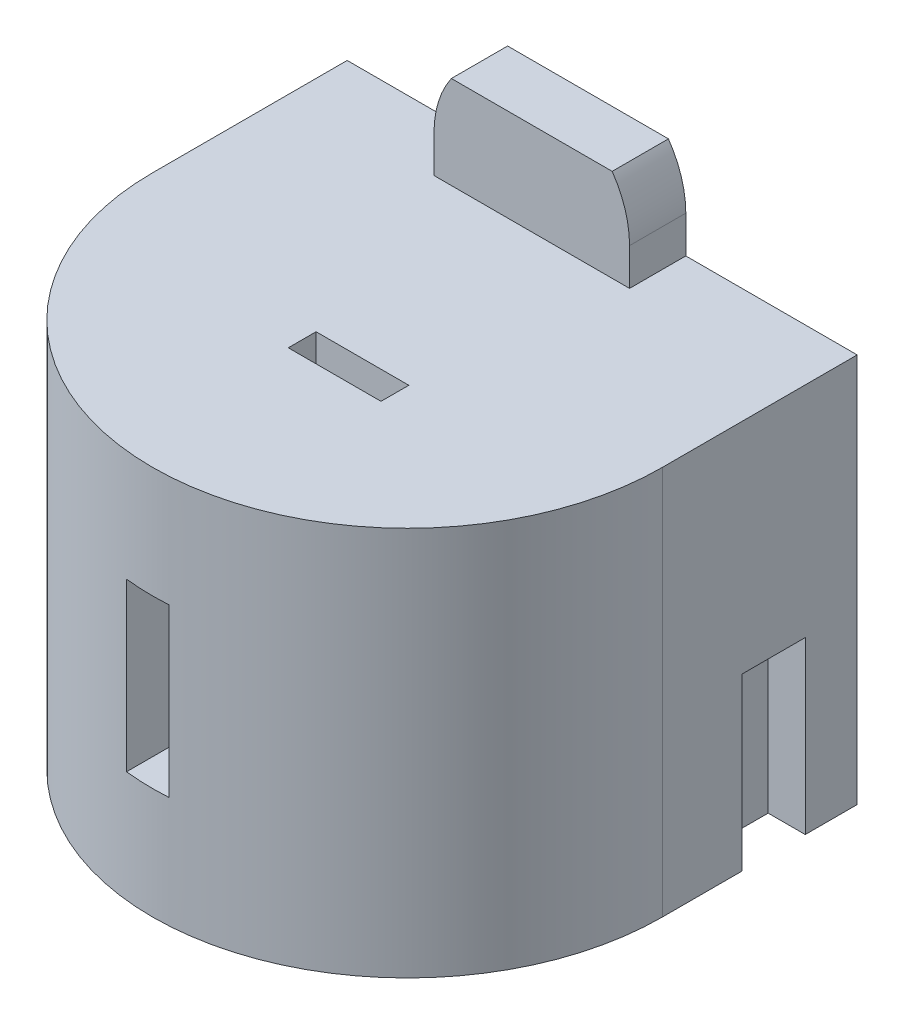
SolidWorks part; units mm, degrees
ref_plane "Спереди" through (0, 0, 0) normal (0, 0, 1) x (1, 0, 0)
ref_plane "Сверху" through (0, 0, 0) normal (0, 1, 0) x (1, 0, 0)
ref_plane "Справа" through (0, 0, 0) normal (1, 0, 0) x (0, 0, -1)
sketch "Эскиз1" plane through (0, 0, 0) normal (0, 0, 1) x (1, 0, 0)
  line L1 (-32.7431, 13.9756) -> (-18.9931, 13.9756)
  line L2 (-18.9931, 13.9756) -> (-18.9931, -7.0244)
  line L3 (-32.7431, -7.0244) -> (-18.9931, -7.0244)
  line L4 (-32.7431, 13.9756) -> (-32.7431, 10.9756)
  line L5 (-21.9931, 10.9756) -> (-21.9931, -4.0244)
  line L6 (-32.7431, -4.0244) -> (-21.9931, -4.0244)
  line L7 (-32.7431, -4.0244) -> (-32.7431, -7.0244)
  line L8 (-32.7431, 10.9756) -> (-21.9931, 10.9756)
  dimension "D1" = 3
  dimension "D2" = 15
  dimension "D3" = 13.75
revolve "Повернуть1" add sketch "Эскиз1" angle 180 about L4
sketch "Эскиз5" plane through (0, 0, 0) normal (0, 0, -1) x (-1, 0, 0)
  line L0 (18.9931, 13.9756) -> (18.9931, -7.0244)
  line L1 (18.9931, -7.0244) -> (46.4931, -7.0244)
  line L2 (46.4931, -7.0244) -> (46.4931, 13.9756)
  line L3 (46.4931, 13.9756) -> (18.9931, 13.9756)
  line L4 (21.9931, 10.9756) -> (21.9931, -4.0244)
  line L5 (21.9931, -4.0244) -> (43.4931, -4.0244)
  line L6 (43.4931, -4.0244) -> (43.4931, 10.9756)
  line L7 (43.4931, 10.9756) -> (21.9931, 10.9756)
  line L8 (21.9931, 10.9756) -> (43.4931, 10.9756) construction
  line L9 (46.4931, 13.9756) -> (18.9931, 13.9756) construction
  line L10 (43.4931, 10.9756) -> (43.4931, -4.0244) construction
  line L11 (43.4931, -4.0244) -> (21.9931, -4.0244) construction
  line L12 (21.9931, 10.9756) -> (21.9931, -4.0244) construction
  line L13 (18.9931, -7.0244) -> (18.9931, 13.9756) construction
  line L14 (46.4931, -7.0244) -> (46.4931, 13.9756) construction
  line L15 (46.4931, -7.0244) -> (18.9931, -7.0244) construction
extrude "Бобышка-Вытянуть1" add sketch "Эскиз5" along normal blind 10.5
sketch "Эскиз6" plane through (0, 0, 0) normal (0, 0, 1) x (1, 0, 0)
  line L1 (-31.8903, -1.022) -> (-34.2218, -1.022)
  line L2 (-31.8903, -1.022) -> (-31.8903, 7.9732)
  line L3 (-31.8903, 7.9732) -> (-34.2218, 7.9732)
  line L4 (-34.2218, -1.022) -> (-34.2218, 7.9732)
  line L5 (-31.8903, -1.022) -> (-34.2218, 7.9732) construction
  line L6 (-31.8903, 7.9732) -> (-34.2218, -1.022) construction
  line L7 (-19.9931, 3.4756) -> (-29.2743, 3.4756) construction
  point P0 (-33.0561, 3.4756)
extrude "Вырез-Вытянуть1" cut sketch "Эскиз6" along normal through all
sketch "Эскиз7" plane through (0, 13.9756, 0) normal (0, 1, 0) x (1, 0, 0)
  line L0 (-32.1622, -3.0071) -> (-32.1622, -4.5071) construction
  line L1 (-34.6622, -3.0071) -> (-29.6622, -3.0071)
  line L2 (-34.6622, -3.0071) -> (-34.6622, -4.5071)
  line L3 (-34.6622, -4.5071) -> (-29.6622, -4.5071)
  line L4 (-29.6622, -3.0071) -> (-29.6622, -4.5071)
extrude "Вырез-Вытянуть2" cut sketch "Эскиз7" against normal through all contours L1 L4 L3 L2
sketch "Эскиз9" plane through (0, 0, -10.5) normal (0, 0, -1) x (-1, 0, 0)
  line L0 (28.2332, 15.9749) -> (28.2332, 13.9766)
  line L1 (38.7784, 15.9749) -> (38.7784, 13.9748)
  line L2 (28.2332, 13.9766) -> (38.7784, 13.9748)
  line L3 (29.1704, 18.9756) -> (37.8412, 18.9756)
  line L4 (113.8713, 18.9756) -> (66.0213, 18.9756) construction
  arc A0 (38.7784, 15.9749) -> (37.8412, 18.9756) centre (33.5058, 15.9749) ccw
  arc A1 (29.1704, 18.9756) -> (28.2332, 15.9749) centre (33.5058, 15.9749) ccw
extrude "Бобышка-Вытянуть2" add sketch "Эскиз9" against normal blind 3.0335 separate body
sketch "Эскиз10" plane through (-46.4931, 0, 0) normal (-1, 0, 0) x (0, 0, 1)
  line L5 (-7.7, 2.1756) -> (-4.3, 2.1756)
  line L6 (-4.3, 2.1756) -> (-4.3, -7.6278)
  line L7 (-7.7, -7.6278) -> (-4.3, -7.6278)
  line L8 (-7.7, 2.1756) -> (-7.7, -7.6278)
extrude "Вырез-Вытянуть3" cut sketch "Эскиз10" against normal blind 2
sketch "Эскиз11" plane through (-18.9931, 0, 0) normal (1, 0, 0) x (0, 0, -1)
  line L5 (7.7, 2.1756) -> (4.3, 2.1756)
  line L6 (4.3, 2.1756) -> (4.3, -8.1699)
  line L7 (7.7, -8.1699) -> (4.3, -8.1699)
  line L8 (7.7, 2.1756) -> (7.7, -8.1699)
extrude "Вырез-Вытянуть4" cut sketch "Эскиз11" against normal blind 2
